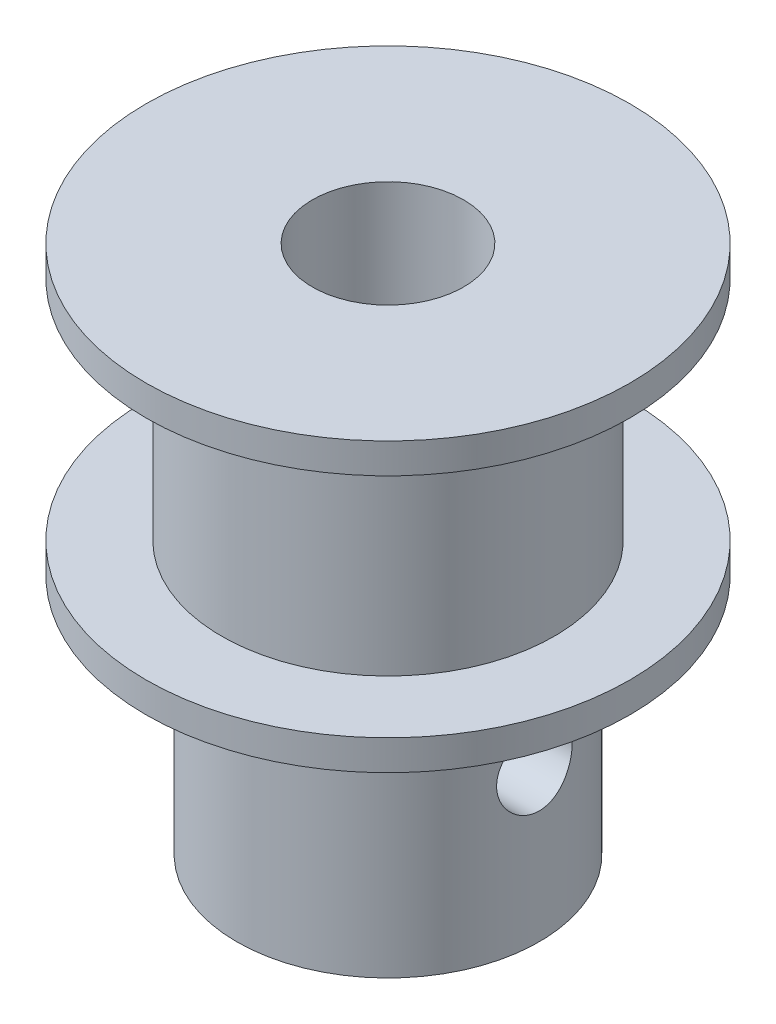
SolidWorks part; units mm, degrees
material "aluminio"
ref_plane "Alzado" through (0, 0, 0) normal (0, 0, 1) x (1, 0, 0)
ref_plane "Planta" through (0, 0, 0) normal (0, 1, 0) x (1, 0, 0)
ref_plane "Vista lateral" through (0, 0, 0) normal (1, 0, 0) x (0, 0, -1)
sketch "Croquis1" plane through (0, 0, 0) normal (0, 0, 1) x (1, 0, 0)
  line L0 (0, 0) -> (0, 36.7556) construction
  line L1 (8, 8) -> (5, 8)
  line L2 (5, 8) -> (5, 0)
  line L3 (2.5, 17.5) -> (8, 17.5)
  line L4 (8, 17.5) -> (8, 16.5)
  line L5 (8, 16.5) -> (5.5, 16.5)
  line L6 (5.5, 16.5) -> (5.5, 9)
  line L7 (5.5, 9) -> (8, 9)
  line L8 (8, 9) -> (8, 8)
  line L9 (5, 0) -> (2.5, 0)
  line L10 (2.5, 0) -> (2.5, 17.5)
  dimension "D1" = 1
  dimension "D2" = 1
  dimension "D3" = 17.5
  dimension "D4" = 5
  dimension "D5" = 11
  dimension "D6" = 16
  dimension "D7" = 16
  dimension "D8" = 10
  dimension "D9" = 9.5
revolve "Revolución1" add sketch "Croquis1" angle 360 about L0
sketch "Croquis2" plane through (0, 0, 0) normal (0, 0, 1) x (1, 0, 0)
  line L0 (-5, 0) -> (5, 0) construction
  circle A0 centre (0, 5) radius 1.25
  dimension "D1" = 5
  dimension "D2" = 2.5
extrude "Cortar-Extruir1" cut sketch "Croquis2" against normal up to next
cosmetic thread "Rosca cosmética2" parameters "D2"=3
pattern_circular "MatrizC1" count 2 over 90 about axis through (0, 0, 0) along (0, -1, 0) of "Cortar-Extruir1"
cosmetic thread "Rosca cosmética1" parameters "D2"=3
